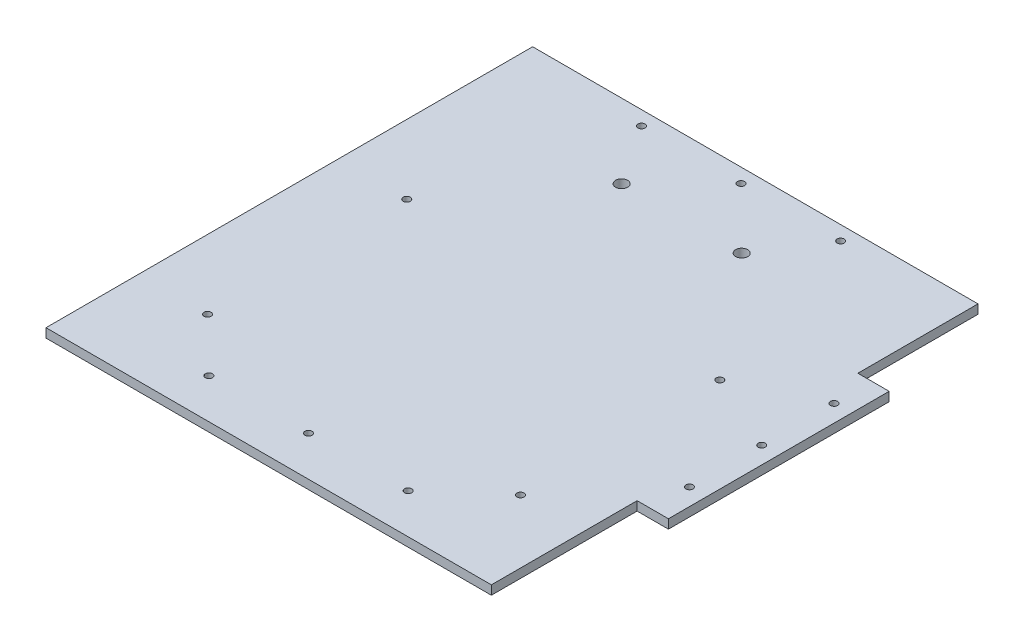
SolidWorks part; units mm, degrees
material "Cedar"
ref_plane "Front Plane" through (0, 0, 0) normal (0, 0, 1) x (1, 0, 0)
ref_plane "Top Plane" through (0, 0, 0) normal (0, 1, 0) x (1, 0, 0)
ref_plane "Right Plane" through (0, 0, 0) normal (1, 0, 0) x (0, 0, -1)
sketch "Sketch1" plane through (0, 0, 0) normal (0, 1, 0) x (1, 0, 0)
  line L0 (72.8376, -16.2766) -> (72.8376, -52.4668) construction
  line L1 (-156.5, -171) -> (156.5, -171)
  line L2 (-156.5, -171) -> (-156.5, 171)
  line L3 (-156.5, 171) -> (156.5, 171)
  line L4 (156.5, -171) -> (156.5, 171)
  line L5 (-156.5, -171) -> (156.5, 171) construction
  line L6 (-156.5, 171) -> (156.5, -171) construction
  point P0 (0, 0)
  dimension "D1" = 342
  dimension "D2" = 313
extrude "Boss-Extrude1" add sketch "Sketch1" against normal blind 6.35
ref_plane "Plane1" through (0, 0, -9) normal (0, 0, -1) x (-1, 0, 0)
sketch "Sketch3" plane through (0, 0, 0) normal (0, 1, 0) x (1, 0, 0)
  line L0 (156.5, 9) -> (-156.5, 9) construction
  line L1 (156.5, -171) -> (156.5, 171) construction
  line L2 (-156.5, 171) -> (-156.5, -171) construction
  line L3 (55, 9) -> (-55, 9) construction
  line L4 (156.5, 86.5702) -> (156.5, -68.5702)
  line L5 (156.5, -68.5702) -> (178.5, -68.5702)
  line L6 (178.5, -68.5702) -> (178.5, 86.5702)
  line L7 (178.5, 86.5702) -> (156.5, 86.5702)
  circle A0 centre (166.5, 9) radius 2.5
  circle A1 centre (166.5, -41.8) radius 2.5
  circle A2 centre (166.5, 59.8) radius 2.5
  point P10 (156.5, 9)
  dimension "D2" = 5
  dimension "D4" = 5
  dimension "D5" = 50.8
  dimension "D1" = 22
  dimension "D3" = 10
extrude "Boss-Extrude2" add sketch "Sketch3" against normal blind 6.35
sketch "Sketch2" plane through (0, 0, 0) normal (0, 1, 0) x (1, 0, 0)
  line L0 (156.5, 9) -> (-156.5, 9) construction
  line L1 (156.5, -171) -> (156.5, -68.5702) construction
  line L2 (-156.5, 171) -> (-156.5, -171) construction
  line L3 (0, -143) -> (0, -171) construction
  line L4 (55, 9) -> (-55, 9) construction
  line L5 (156.5, -143) -> (-156.5, -143) construction
  line L6 (-156.5, -171) -> (156.5, -171) construction
  circle A0 centre (0, -143) radius 2.5
  circle A1 centre (-70, -143) radius 2.5
  circle A2 centre (70, -143) radius 2.5
  circle A3 centre (-70, 161) radius 2.5
  circle A4 centre (0, 161) radius 2.5
  circle A5 centre (70, 161) radius 2.5
  dimension "D2" = 5
  dimension "D3" = 5
  dimension "D4" = 70
  dimension "D1" = 152
extrude "Cut-Extrude1" cut sketch "Sketch2" against normal through all
sketch "Sketch4" plane through (0, 0, 0) normal (0, 1, 0) x (1, 0, 0)
  circle A15 centre (42.5742, 118.8674) radius 4.25
  circle A16 centre (-41.83, 118.8674) radius 4.25
  circle A17 centre (-107.9115, -106.0655) radius 2.5
  circle A18 centre (-107.9115, 33.9345) radius 2.5
  circle A19 centre (112.0885, 33.9345) radius 2.5
  circle A20 centre (112.0885, -106.0655) radius 2.5
extrude "Cut-Extrude2" cut sketch "Sketch4" against normal through all
